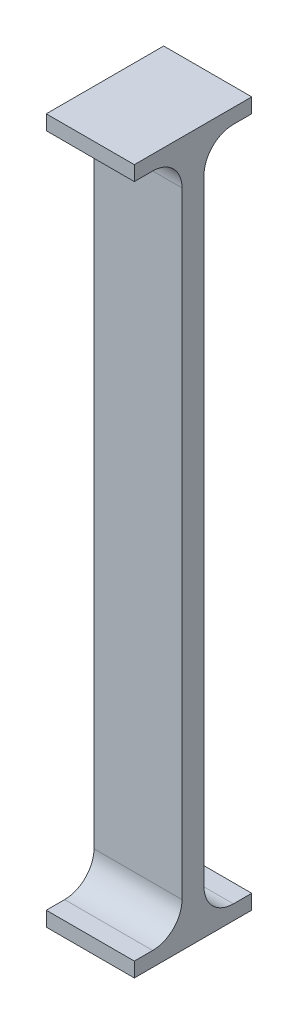
SolidWorks part; units mm, degrees
ref_plane "Front Plane" through (0, 0, 0) normal (0, 0, 1) x (1, 0, 0)
ref_plane "Top Plane" through (0, 0, 0) normal (0, 1, 0) x (1, 0, 0)
ref_plane "Right Plane" through (0, 0, 0) normal (1, 0, 0) x (0, 0, -1)
sketch "Sketch1" plane through (0, 0, 0) normal (0, 0, 1) x (1, 0, 0)
  line L1 (-15, 0) -> (15, 0)
  line L2 (-15, 0) -> (-15, 239.95)
  line L3 (-15, 239.95) -> (15, 239.95)
  line L4 (15, 0) -> (15, 239.95)
  point P4 (0, 0)
  dimension "D1" = 30
  dimension "D2" = 239.95
extrude "Boss-Extrude1" add sketch "Sketch1" along normal mid plane 7.5
sketch "Sketch2" plane through (0, 0, 0) normal (0, 0, 1) x (1, 0, 0)
  line L0 (15, 0) -> (15, 239.95) construction
  line L1 (-15, 0) -> (15, 0)
  line L2 (-15, 0) -> (-15, 5)
  line L3 (-15, 5) -> (15, 5)
  line L4 (15, 0) -> (15, 5)
  dimension "D1" = 5
extrude "Boss-Extrude2" add sketch "Sketch2" along normal mid plane 40
sketch "Sketch3" plane through (0, 0, 0) normal (0, 0, 1) x (1, 0, 0)
  line L0 (15, 5) -> (15, 239.95) construction
  line L1 (-15, 239.95) -> (15, 239.95)
  line L2 (-15, 239.95) -> (-15, 234.95)
  line L3 (-15, 234.95) -> (15, 234.95)
  line L4 (15, 239.95) -> (15, 234.95)
  dimension "D1" = 5
extrude "Boss-Extrude3" add sketch "Sketch3" along normal mid plane 40
fillet "Fillet1" radius 10 2 edges at (0, 234.95, -3.75) (0, 234.95, 3.75)
fillet "Fillet2" radius 10 2 edges at (0, 5, -3.75) (0, 5, 3.75)
